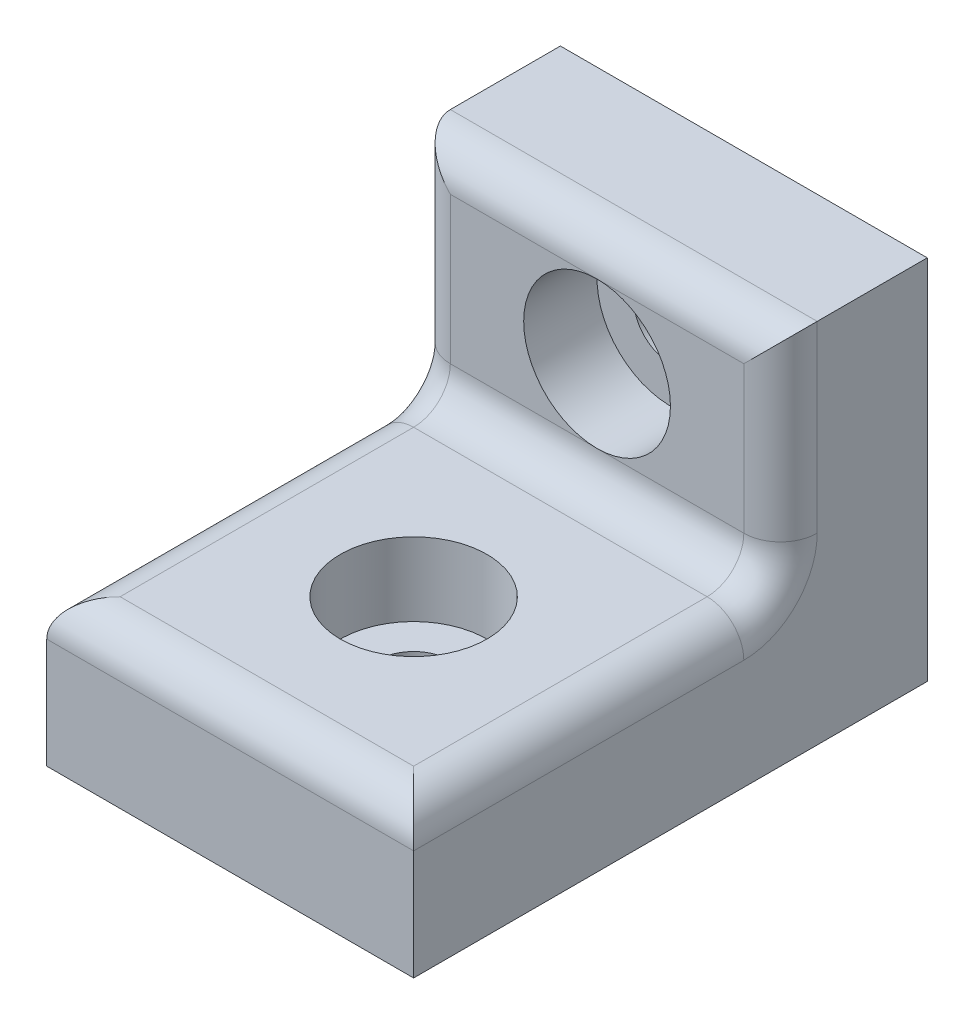
SolidWorks part; units mm, degrees
ref_plane "Plan de face" through (0, 0, 0) normal (0, 0, 1) x (1, 0, 0)
ref_plane "Plan de dessus" through (0, 0, 0) normal (0, 1, 0) x (1, 0, 0)
ref_plane "Plan de droite" through (0, 0, 0) normal (1, 0, 0) x (0, 0, -1)
sketch "Esquisse1" plane through (0, 0, 0) normal (0, 0, 1) x (1, 0, 0)
  line L1 (-5, 10) -> (5, 10)
  line L2 (-5, 10) -> (-5, 0)
  line L3 (-5, 0) -> (5, 0)
  line L4 (5, 10) -> (5, 0)
  dimension "D1" = 10
  dimension "D2" = 10
  dimension "D3" = 5
extrude "Boss.-Extru.1" add sketch "Esquisse1" along normal blind 4
sketch "Esquisse2" plane through (0, 0, 4) normal (0, 0, 1) x (1, 0, 0)
  line L0 (5, 0) -> (5, 10) construction
  line L1 (-5, 0) -> (5, 0)
  line L2 (-5, 0) -> (-5, 4)
  line L3 (-5, 4) -> (5, 4)
  line L4 (5, 0) -> (5, 4)
  dimension "D1" = 4
extrude "Boss.-Extru.2" add sketch "Esquisse2" along normal blind 10
sketch "Esquisse3" plane through (0, 0, 4) normal (0, 0, 1) x (1, 0, 0)
  line L0 (5, 10) -> (-5, 10) construction
  line L1 (-5, 10) -> (-5, 4) construction
  circle A0 centre (0, 7) radius 1
  point P2 (0, 10)
  point P3 (-5, 7)
  dimension "D1" = 2
extrude "Enlèv. mat.-Extru.1" cut sketch "Esquisse3" against normal through all
fillet "Congé1" radius 1 7 edges at (0, 4, 4) (5, 7, 4) (-5, 7, 4) (0, 4, 14) (5, 4, 9) (-5, 4, 9) (0, 10, 4)
sketch "Esquisse4" plane through (0, 4, 0) normal (0, 1, 0) x (1, 0, 0)
  line L0 (5, -14) -> (-5, -14) construction
  line L1 (-5, -14) -> (-5, -4) construction
  circle A0 centre (0, -9) radius 1
  point P0 (0, -14)
  point P1 (-5, -9)
  dimension "D1" = 2
extrude "Enlèv. mat.-Extru.2" cut sketch "Esquisse4" against normal through all
sketch "Esquisse5" plane through (0, 0, 4) normal (0, 0, 1) x (1, 0, 0)
  circle A0 centre (0, 7) radius 2
  dimension "D1" = 4
extrude "Enlèv. mat.-Extru.3" cut sketch "Esquisse5" against normal blind 2
sketch "Esquisse6" plane through (0, 4, 0) normal (0, 1, 0) x (1, 0, 0)
  circle A0 centre (0, -9) radius 2
  dimension "D1" = 4
extrude "Enlèv. mat.-Extru.4" cut sketch "Esquisse6" against normal blind 2
